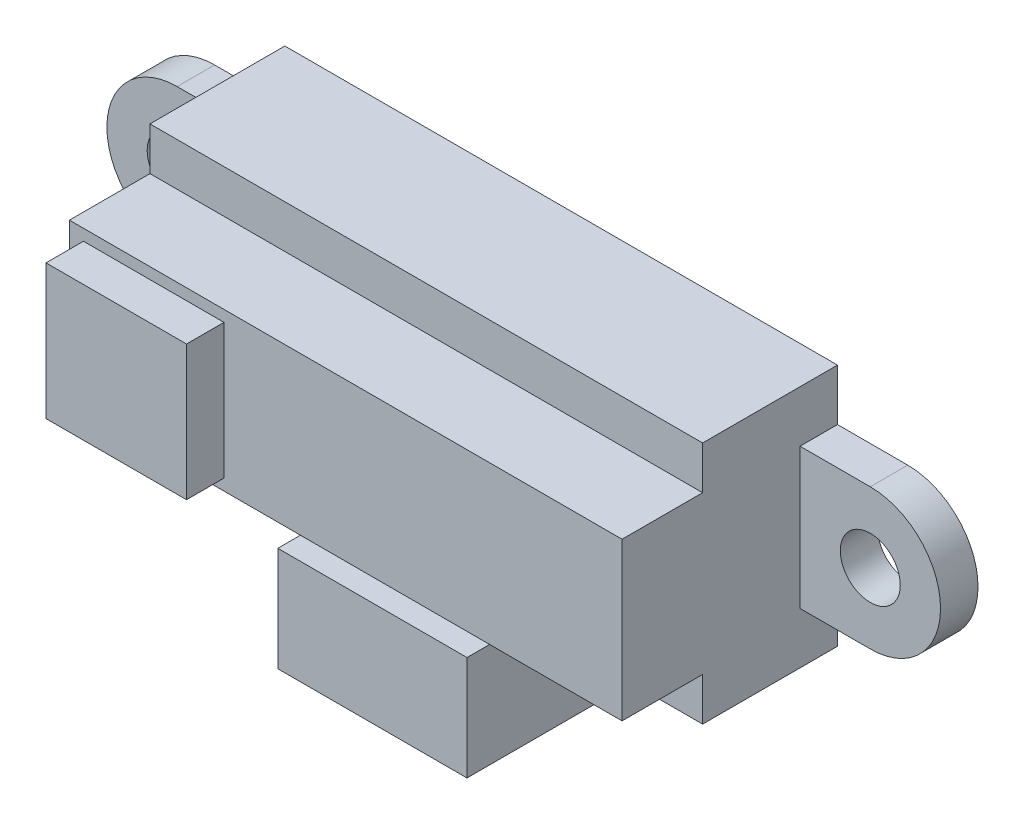
SolidWorks part; units mm, degrees
ref_plane "Plan de face" through (0, 0, 0) normal (0, 0, 1) x (1, 0, 0)
ref_plane "Plan de dessus" through (0, 0, 0) normal (0, 1, 0) x (1, 0, 0)
ref_plane "Plan de droite" through (0, 0, 0) normal (1, 0, 0) x (0, 0, -1)
sketch "Esquisse1" plane through (0, 0, 0) normal (0, 0, 1) x (1, 0, 0)
  line L0 (-14.75, 6.5) -> (14.75, -6.5) construction
  line L1 (-14.75, 6.5) -> (14.75, 6.5)
  line L2 (-14.75, 6.5) -> (-14.75, -6.5)
  line L3 (-14.75, -6.5) -> (14.75, -6.5)
  line L4 (14.75, 6.5) -> (14.75, -6.5)
  line L5 (14.75, 6.5) -> (-14.75, -6.5) construction
  point P4 (0, 0)
  point P5 (0, 0)
  dimension "D1" = 29.5
  dimension "D2" = 13
extrude "Boss.-Extru.2" add sketch "Esquisse1" along normal blind 7.2
sketch "Esquisse2" plane through (0, 0, 7.2) normal (0, 0, 1) x (1, 0, 0)
  line L0 (-14.75, 4.2) -> (14.75, 4.2)
  line L1 (-14.75, 6.5) -> (-14.75, -6.5) construction
  line L2 (14.75, -6.5) -> (14.75, 6.5) construction
  line L3 (-14.75, 0) -> (14.75, 0) construction
  line L4 (14.75, 6.5) -> (-14.75, 6.5) construction
  line L5 (-14.75, -4.2) -> (14.75, -4.2)
  line L6 (-14.75, 4.2) -> (-14.75, -4.2)
  line L7 (14.75, -4.2) -> (14.75, 4.2)
  point P12 (-14.75, 0)
  dimension "D1" = 2.3
extrude "Boss.-Extru.3" add sketch "Esquisse2" along normal blind 4.3 contours L7 L0 L6 L5
sketch "Esquisse4" plane through (0, 0, 11.5) normal (0, 0, 1) x (1, 0, 0)
  line L0 (-14, -3.6) -> (-6.5, -3.6)
  line L1 (-6.5, -3.6) -> (-6.5, 3.6)
  line L2 (-6.5, 3.6) -> (-14, 3.6)
  line L3 (-14, 3.6) -> (-14, -3.6)
  line L4 (-14.75, 4.2) -> (-14.75, -4.2) construction
  line L5 (-14.75, 4.2) -> (14.75, 4.2) construction
  dimension "D1" = 0.75
  dimension "D2" = 0.6
  dimension "D3" = 7.5
  dimension "D4" = 7.2
extrude "Boss.-Extru.4" add sketch "Esquisse4" along normal blind 2
sketch "Esquisse7" plane through (0, -6.5, 0) normal (0, -1, 0) x (-1, 0, 0)
  line L0 (14.75, -3.3) -> (-14.75, -3.3) construction
  line L3 (0, 0) -> (0, -7.2) construction
  line L4 (14.75, -7.2) -> (-14.75, -7.2) construction
  line L5 (14.75, -7.2) -> (14.75, 0) construction
  line L6 (-14.75, -7.2) -> (-14.75, 0) construction
  line L7 (14.75, 0) -> (-14.75, 0) construction
  point P13 (0, -3.3)
  dimension "D1" = 3.3
ref_plane "Plan1" through (0, 0, 3.3) normal (0, 0, 1) x (1, 0, 0)
sketch "Esquisse8" plane through (0, 0, 3.3) normal (0, 0, 1) x (1, 0, 0)
  line L1 (-5.05, -12.4) -> (5.05, -12.4)
  line L2 (5.05, -12.4) -> (5.05, -6.5)
  line L3 (-14.75, -6.5) -> (14.75, -6.5) construction
  line L4 (5.05, -6.5) -> (-5.05, -6.5)
  line L5 (-5.05, -12.4) -> (-5.05, -6.5)
  line L6 (0, -6.5) -> (0, -12.4) construction
  dimension "D1" = 10.1
  dimension "D2" = 18.9
extrude "Boss.-Extru.5" add sketch "Esquisse8" along normal blind 1.2
sketch "Esquisse9" plane through (5.05, 0, 0) normal (1, 0, 0) x (0, 0, -1)
  line L0 (-4.5, -12.4) -> (-10.0771, -12.4)
  line L1 (-10.0771, -12.4) -> (-10.0771, -6.8305)
  line L2 (-10.0771, -6.8305) -> (-8.5089, -6.8305)
  line L3 (-8.5089, -6.8305) -> (-7.2, -5.9603)
  line L4 (-7.2, -6.5) -> (-7.2, -4.2) construction
  line L5 (-7.2, -5.9603) -> (-7.2, -6.5)
  line L6 (-7.2, -6.5) -> (-4.5, -6.5)
  line L7 (-4.5, -6.5) -> (-4.5, -12.4)
  point P4 (-10.0771, -6.4752)
  point P13 (0, 0)
  point P14 (-7.2, -5.683)
  point P15 (-7.2, -5.9603)
  point P16 (-8.5089, -6.8149)
  point P17 (-8.5089, -6.8305)
  dimension "D1" = 5.5771
  dimension "D2" = 1.5683
  dimension "D3" = 0.5397
  dimension "D4" = 5.5695
extrude "Boss.-Extru.6" add sketch "Esquisse9" against normal up to vertex
sketch "Esquisse10" plane through (0, 0, 0) normal (0, 0, 1) x (1, 0, 0)
  line L0 (18.5, 3.75) -> (14.75, 3.75)
  line L1 (14.75, -4.2) -> (14.75, 4.2) construction
  line L7 (14.75, 0) -> (14.75, 3.75)
  line L9 (18.5, -3.75) -> (14.75, -3.75)
  line L11 (14.75, 0) -> (14.75, -3.75)
  line L14 (0, 0) -> (0, 7.7471) construction
  line L15 (-18.5, -3.75) -> (-14.75, -3.75)
  line L16 (-18.5, 3.75) -> (-14.75, 3.75)
  line L17 (-14.75, 0) -> (-14.75, 3.75)
  line L18 (-14.75, 0) -> (-14.75, -3.75)
  arc A2 (18.5, -3.75) -> (18.5, 3.75) centre (18.5, 0) ccw
  circle A3 centre (18.5, 0) radius 1.6
  arc A4 (-18.5, -3.75) -> (-18.5, 3.75) centre (-18.5, 0) cw
  circle A5 centre (-18.5, 0) radius 1.6
  point P2 (14.75, 0)
  point P4 (14.75, 0)
  dimension "D1" = 7.5
  dimension "D2" = 3.2
extrude "Boss.-Extru.8" add sketch "Esquisse10" along normal blind 2
